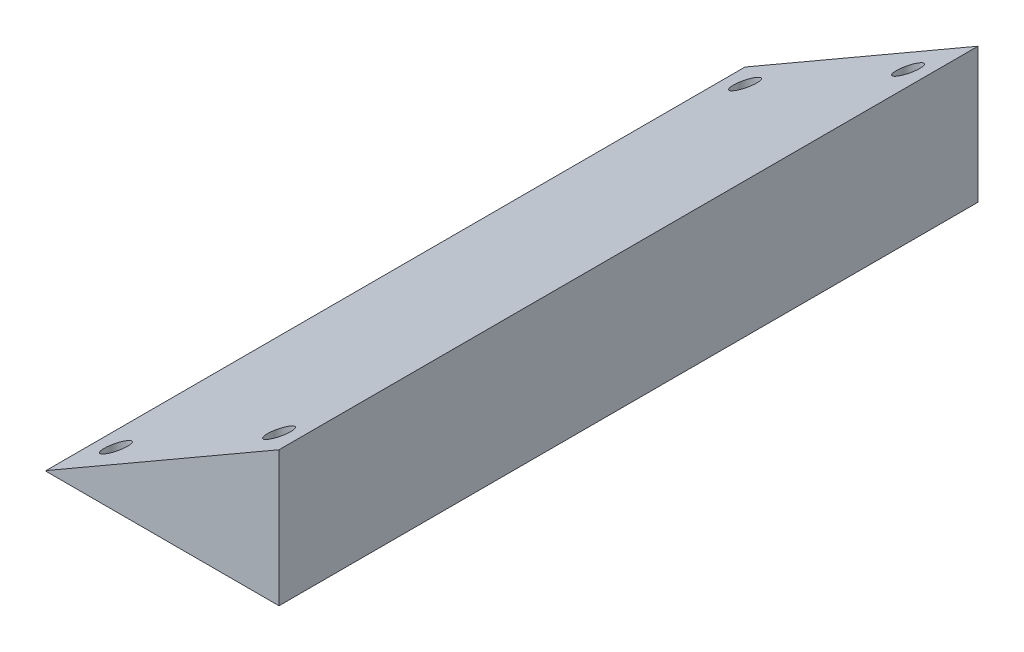
SolidWorks part; units mm, degrees
material "Acrylic (Medium-high impact)"
ref_plane "Front Plane" through (0, 0, 0) normal (0, 0, 1) x (1, 0, 0)
ref_plane "Top Plane" through (0, 0, 0) normal (0, 1, 0) x (1, 0, 0)
ref_plane "Right Plane" through (0, 0, 0) normal (1, 0, 0) x (0, 0, -1)
sketch "Sketch2" plane through (0, 0, 0) normal (0, 0, 1) x (1, 0, 0)
  line L0 (-25, 0) -> (25, 0)
  line L1 (25, 0) -> (25, 29)
  line L2 (25, 29) -> (-25, 0.1325)
  line L3 (-25, 0.1325) -> (-25, 0)
  dimension "D1" = 50
  dimension "D2" = 60
  dimension "D3" = 29
  dimension "D4" = 0
  dimension "D5" = 25
extrude "Boss-Extrude1" add sketch "Sketch2" along normal mid plane 150
sketch "Sketch3" plane through (0, 0, 0) normal (0, -1, 0) x (1, 0, 0)
  line L0 (-25, 75) -> (-25, -75) construction
  line L1 (25, 75) -> (25, -75) construction
  line L2 (-25, -75) -> (25, -75) construction
  line L3 (-25, 75) -> (25, 75) construction
  circle A0 centre (-17.5, 67.5) radius 2.5
  circle A1 centre (17.5, 67.5) radius 2.5
  circle A2 centre (-17.5, -67.5) radius 2.5
  circle A3 centre (17.5, -67.5) radius 2.5
  point P0 (-17.5, 67.5)
  point P1 (17.5, 67.5)
  point P2 (17.5, -67.5)
  point P3 (-17.5, -67.5)
  dimension "D1" = 7.5
  dimension "D2" = 7.5
  dimension "D3" = 7.5
  dimension "D4" = 7.5
  dimension "D5" = 7.5
  dimension "D6" = 7.5
  dimension "D7" = 7.5
  dimension "D8" = 7.5
extrude "Cut-Extrude1" cut sketch "Sketch3" against normal blind 50
